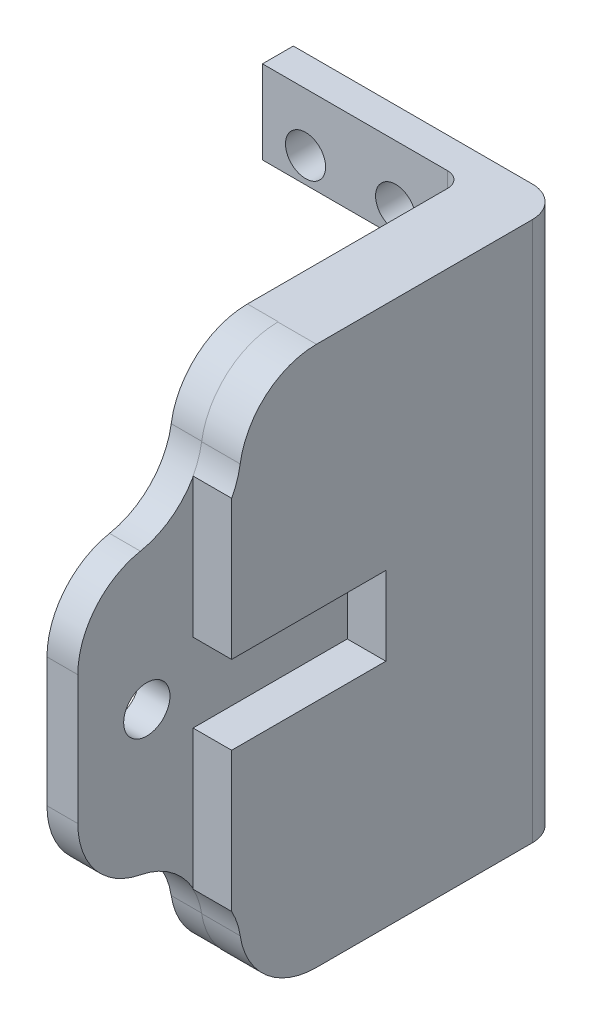
SolidWorks part; units mm, degrees
ref_plane "Plan de face" through (0, 0, 0) normal (0, 0, 1) x (1, 0, 0)
ref_plane "Plan de dessus" through (0, 0, 0) normal (0, 1, 0) x (1, 0, 0)
ref_plane "Plan de droite" through (0, 0, 0) normal (1, 0, 0) x (0, 0, -1)
ref_plane "Plan1" through (17.5, 0, 0) normal (1, 0, 0) x (0, 0, -1)
sketch "Esquisse1" plane through (17.5, 0, 0) normal (1, 0, 0) x (0, 0, -1)
  line L0 (-7, 0) -> (-7, 35)
  line L1 (-12.5, 29.1009) -> (-12.5, 5.8991)
  arc A0 (-11.9434, 4.25) -> (-7, 0) centre (-7, 5) ccw
  arc A1 (-7, 35) -> (-11.9434, 30.75) centre (-7, 30) ccw
  arc A2 (-11.9434, 30.75) -> (-12.5, 29.1009) centre (-16.8869, 31.5) cw
  arc A3 (-12.5, 5.8991) -> (-11.9434, 4.25) centre (-16.8869, 3.5) cw
extrude "Boss.-Extru.1" add sketch "Esquisse1" against normal blind 2.5
sketch "Esquisse2" plane through (0, 0, 7) normal (0, 0, -1) x (-1, 0, 0)
  line L0 (-15, 0) -> (-17.5, 0)
  line L1 (-17.5, 0) -> (-17.5, 35)
  line L2 (-17.5, 35) -> (-15, 35)
  line L3 (-15, 35) -> (-15, 0)
extrude "Boss.-Extru.2" add sketch "Esquisse2" along normal blind 16
sketch "Esquisse3" plane through (15, 0, 0) normal (-1, 0, 0) x (0, 0, 1)
  line L0 (19.9743, 21.6796) -> (19.9743, 13.3204)
  line L1 (6.9743, 0) -> (-9, 0)
  line L2 (-9, 0) -> (-9, 35)
  line L3 (-9, 35) -> (6.9743, 35)
  arc A0 (6.9743, 35) -> (11.9177, 30.75) centre (6.9743, 30) cw
  arc A1 (11.9177, 30.75) -> (15.9177, 26.5898) centre (16.8612, 31.5) ccw
  arc A2 (15.9177, 26.5898) -> (19.9743, 21.6796) centre (14.9743, 21.6796) cw
  arc A3 (19.9743, 13.3204) -> (15.9177, 8.4102) centre (14.9743, 13.3204) cw
  arc A4 (15.9177, 8.4102) -> (11.9177, 4.25) centre (16.8612, 3.5) ccw
  arc A5 (11.9177, 4.25) -> (6.9743, 0) centre (6.9743, 5) cw
  dimension "D5" = 28
  dimension "D6" = 8.3593
  dimension "D7" = 25
  dimension "D8" = 3.1131
  dimension "D9" = 9.8204
  dimension "D10" = 9.8204
  dimension "D11" = 8
  dimension "D12" = 8
  dimension "D3" = 8.0566
  dimension "D4" = 18.1796
extrude "Boss.-Extru.3" add sketch "Esquisse3" along normal blind 2
sketch "Esquisse4" plane through (13, 0, 0) normal (-1, 0, 0) x (0, 0, 1)
  line L0 (-7, 0) -> (-9, 0)
  line L1 (-9, 0) -> (-9, 35)
  line L2 (-9, 35) -> (-7, 35)
  line L3 (-7, 35) -> (-7, 0)
  line L5 (-9, 35) -> (-9, 0) construction
  dimension "D1" = 2
extrude "Boss.-Extru.4" add sketch "Esquisse4" along normal blind 13
sketch "Esquisse5" plane through (17.5, 0, 0) normal (1, 0, 0) x (0, 0, -1)
  line L0 (-2.5, 20.05) -> (-12.5, 20.05)
  line L1 (-12.5, 20.05) -> (-12.5, 14.95)
  line L2 (-12.5, 14.95) -> (-2.5, 14.95)
  line L3 (-2.5, 14.95) -> (-2.5, 20.05)
extrude "Enlèv. mat.-Extru.1" cut sketch "Esquisse5" against normal blind 2.5
sketch "Esquisse6" plane through (0, 0, -7) normal (0, 0, 1) x (1, 0, 0)
  line L0 (0, 29.6) -> (0, 5.4)
  line L1 (0, 5.4) -> (11.43, 5.4)
  line L2 (11.43, 5.4) -> (11.43, 29.6)
  line L3 (11.43, 29.6) -> (0, 29.6)
extrude "Enlèv. mat.-Extru.2" cut sketch "Esquisse6" against normal through all
hole_wizard "Diamètre du perçage Ø2.6 (2.6)1" positions "Esquisse8" profile "Esquisse7" hole size "Ø2.6" standard "Ansi Métrique"
sketch "Esquisse8" plane through (0, 0, -9) normal (0, 0, -1) x (-1, 0, 0)
  point P0 (-8.5936, 3.75)
  point P1 (-8.636, 31.25)
  point P2 (-2.794, 31.25)
  point P3 (-2.8364, 3.75)
sketch "Esquisse7" plane through (8.5936, 3.75, -9) normal (1, 0, 0) x (0, 1, 0)
  line L0 (0, 0) -> (0, 28.9743)
  line L1 (0, 28.9743) -> (1.3, 28.9743)
  line L2 (1.3, 28.9743) -> (1.3, 0)
  line L5 (1.3, 0) -> (0, 0)
  line L11 (0, -6.35) -> (0, 107.95) construction
  dimension "Diamètre du perçage jusqu'au prochain" = 2.6
  dimension "Profondeur du perçage jusqu'au prochain" = 28.9743
hole_wizard "Diamètre du perçage Ø3.0 (3)1" positions "Esquisse10" profile "Esquisse9" hole size "Ø3.0" standard "Ansi Métrique"
sketch "Esquisse10" plane through (13, 0, 0) normal (-1, 0, 0) x (0, 0, 1)
  point P0 (15.5, 17.5)
sketch "Esquisse9" plane through (13, 17.5, 15.5) normal (0, 1, 0) x (0, 0, 1)
  line L0 (0, 0) -> (0, 4.5)
  line L1 (0, 4.5) -> (1.5, 4.5)
  line L2 (1.5, 4.5) -> (1.5, 0)
  line L5 (1.5, 0) -> (0, 0)
  line L11 (0, -6.35) -> (0, 107.95) construction
  dimension "Diamètre du perçage jusqu'au prochain" = 3
  dimension "Profondeur du perçage jusqu'au prochain" = 4.5
fillet "Congé1" radius 1 1 edges
fillet "Congé2" radius 2 1 edges at (17.5, 17.5, -9)
